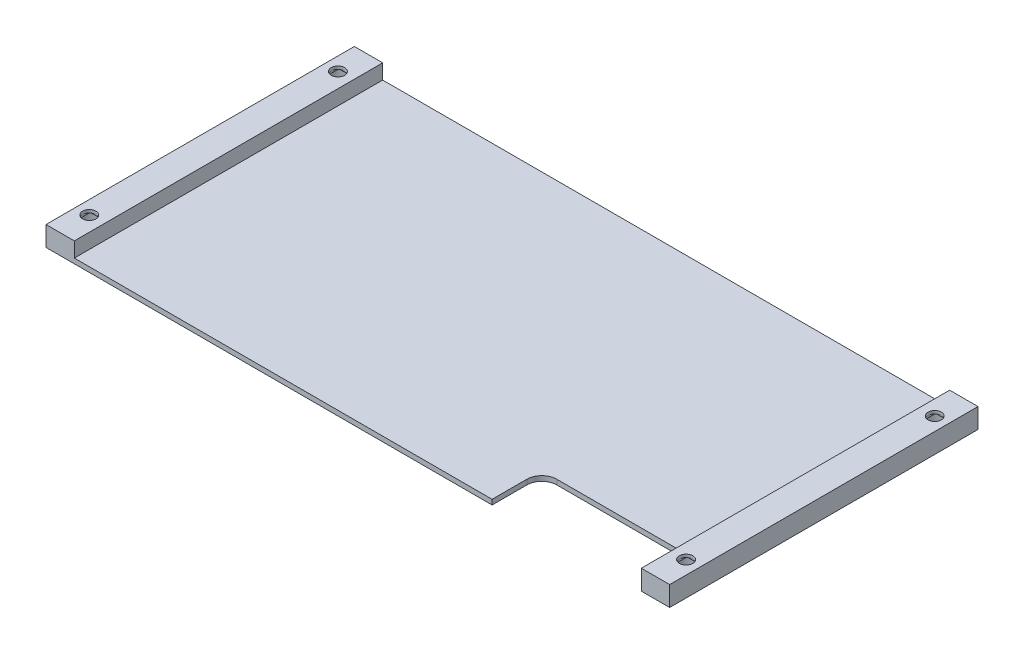
SolidWorks part; units mm, degrees
ref_plane "Front Plane" through (0, 0, 0) normal (0, 0, 1) x (1, 0, 0)
ref_plane "Top Plane" through (0, 0, 0) normal (0, 1, 0) x (1, 0, 0)
ref_plane "Right Plane" through (0, 0, 0) normal (1, 0, 0) x (0, 0, -1)
sketch "Sketch1" plane through (0, 0, 0) normal (0, 1, 0) x (1, 0, 0)
  line L1 (-63, -31) -> (63, -31)
  line L2 (-63, -31) -> (-63, 31)
  line L3 (-63, 31) -> (63, 31)
  line L4 (63, -31) -> (63, 31)
  line L5 (-63, -31) -> (63, 31) construction
  line L6 (-63, 31) -> (63, -31) construction
  point P0 (0, 0)
  dimension "D1" = 126
  dimension "D2" = 62
extrude "Boss-Extrude1" add sketch "Sketch1" along normal blind 1
sketch "Sketch2" plane through (0, 1, 0) normal (0, 1, 0) x (1, 0, 0)
  line L0 (-63, -31) -> (63, -31) construction
  line L1 (-63, 31) -> (-57, 31)
  line L2 (-63, 31) -> (-63, -31)
  line L3 (-63, -31) -> (-57, -31)
  line L4 (-57, 31) -> (-57, -31)
  line L6 (63, 31) -> (57, 31)
  line L7 (63, 31) -> (63, -31)
  line L8 (63, -31) -> (57, -31)
  line L9 (57, 31) -> (57, -31)
  dimension "D1" = 6
extrude "Boss-Extrude2" add sketch "Sketch2" along normal blind 3
sketch "Sketch3" plane through (0, 4, 0) normal (0, 1, 0) x (1, 0, 0)
  line L0 (-63, 31) -> (-57, -31) construction
  line L1 (-60, -25) -> (-60, 25) construction
  line L2 (0, 0) -> (0, 31) construction
  line L3 (57, 31) -> (-57, 31) construction
  line L4 (60, -25) -> (60, 25) construction
  line L5 (63, 31) -> (57, -31) construction
  circle A0 centre (-60, 25) radius 1.35
  circle A1 centre (-60, -25) radius 1.35
  circle A2 centre (60, -25) radius 1.35
  circle A3 centre (60, 25) radius 1.35
  point P7 (-60, 0)
  point P20 (60, 0)
  dimension "D1" = 2.7
  dimension "D2" = 50
extrude "Cut-Extrude1" cut sketch "Sketch3" against normal through all
sketch "Sketch4" plane through (0, 0, 0) normal (0, -1, 0) x (1, 0, 0)
  circle A0 centre (60, -25) radius 2.5
  circle A1 centre (60, 25) radius 2.5
  circle A2 centre (-60, 25) radius 2.5
  circle A3 centre (-60, -25) radius 2.5
  dimension "D1" = 5
extrude "Cut-Extrude2" cut sketch "Sketch4" against normal blind 3
sketch "Sketch5" plane through (0, 0, 0) normal (0, -1, 0) x (1, 0, 0)
  line L0 (-63, 31) -> (63, 31) construction
  line L1 (57, 31) -> (27, 31)
  line L2 (57, 31) -> (57, 21)
  line L3 (57, 21) -> (27, 21)
  line L4 (27, 31) -> (27, 21)
  line L6 (57, -31) -> (57, 31) construction
  dimension "D1" = 30
  dimension "D2" = 10
extrude "Cut-Extrude3" cut sketch "Sketch5" against normal through all
fillet "Fillet1" radius 3 2 edges at (27, 0.5, 21) (57, 0.5, 21)
sketch "Sketch6" plane through (0, 3, 0) normal (0, -1, 0) x (1, 0, 0)
  line L2 (-61.35, 22.8958) -> (-61.35, 27.1042)
  line L4 (-58.65, 22.8958) -> (-58.65, 27.1042)
  line L5 (-61.35, 22.8958) -> (-58.65, 27.1042) construction
  line L6 (-61.35, 27.1042) -> (-58.65, 22.8958) construction
  line L8 (-61.35, -27.1042) -> (-61.35, -22.8958)
  line L10 (-58.65, -27.1042) -> (-58.65, -22.8958)
  line L11 (-61.35, -27.1042) -> (-58.65, -22.8958) construction
  line L12 (-61.35, -22.8958) -> (-58.65, -27.1042) construction
  circle A0 centre (-60, 25) radius 2.5 construction
  arc A1 (-58.65, 27.1042) -> (-61.35, 27.1042) centre (-60, 25) ccw
  circle A2 centre (-60, 25) radius 1.35 construction
  arc A3 (-61.35, 22.8958) -> (-58.65, 22.8958) centre (-60, 25) ccw
  circle A4 centre (-60, -25) radius 2.5 construction
  arc A5 (-58.65, -22.8958) -> (-61.35, -22.8958) centre (-60, -25) ccw
  circle A6 centre (-60, -25) radius 1.35 construction
  arc A7 (-61.35, -27.1042) -> (-58.65, -27.1042) centre (-60, -25) ccw
  point P0 (-60, 25)
  point P8 (-60, -25)
extrude "Cut-Extrude4" cut sketch "Sketch6" against normal blind 0.2
sketch "Sketch7" plane through (0, 3.2, 0) normal (0, -1, 0) x (1, 0, 0)
  line L0 (-58.65, -25) -> (-58.65, -22.8958) construction
  line L1 (-61.35, -26.35) -> (-58.65, -26.35)
  line L2 (-61.35, -26.35) -> (-61.35, -23.65)
  line L3 (-61.35, -23.65) -> (-58.65, -23.65)
  line L4 (-58.65, -26.35) -> (-58.65, -23.65)
  line L5 (-61.35, -26.35) -> (-58.65, -23.65) construction
  line L6 (-61.35, -23.65) -> (-58.65, -26.35) construction
  line L7 (-58.65, 22.8958) -> (-58.65, 27.1042) construction
  line L8 (-61.35, 23.65) -> (-58.65, 23.65)
  line L9 (-61.35, 23.65) -> (-61.35, 26.35)
  line L10 (-61.35, 26.35) -> (-58.65, 26.35)
  line L11 (-58.65, 23.65) -> (-58.65, 26.35)
  line L12 (-61.35, 23.65) -> (-58.65, 26.35) construction
  line L13 (-61.35, 26.35) -> (-58.65, 23.65) construction
  arc A0 (-58.65, -25) -> (-61.35, -25) centre (-60, -25) ccw construction
  arc A1 (-58.65, 25) -> (-61.35, 25) centre (-60, 25) ccw construction
  point P0 (-60, -25)
  point P11 (-60, 25)
extrude "Cut-Extrude5" cut sketch "Sketch7" against normal blind 0.2
mirror "Mirror1" about plane through (0, 0, 0) normal (1, 0, 0) of "Cut-Extrude5", "Cut-Extrude4"
sketch "Sketch8" plane through (0, 4, 0) normal (0, 1, 0) x (1, 0, 0)
  line L0 (-63, -31) -> (-57, -31) construction
  line L1 (-63, 31) -> (-62.7, 31)
  line L2 (-63, 31) -> (-63, -31)
  line L3 (-63, -31) -> (-62.7, -31)
  line L4 (-62.7, 31) -> (-62.7, -31)
  line L5 (57, -31) -> (63, -31) construction
  line L6 (63, 31) -> (62.7, 31)
  line L7 (63, 31) -> (63, -31)
  line L8 (63, -31) -> (62.7, -31)
  line L9 (62.7, 31) -> (62.7, -31)
  dimension "D1" = 0.3
extrude "Cut-Extrude6" cut sketch "Sketch8" against normal through all
